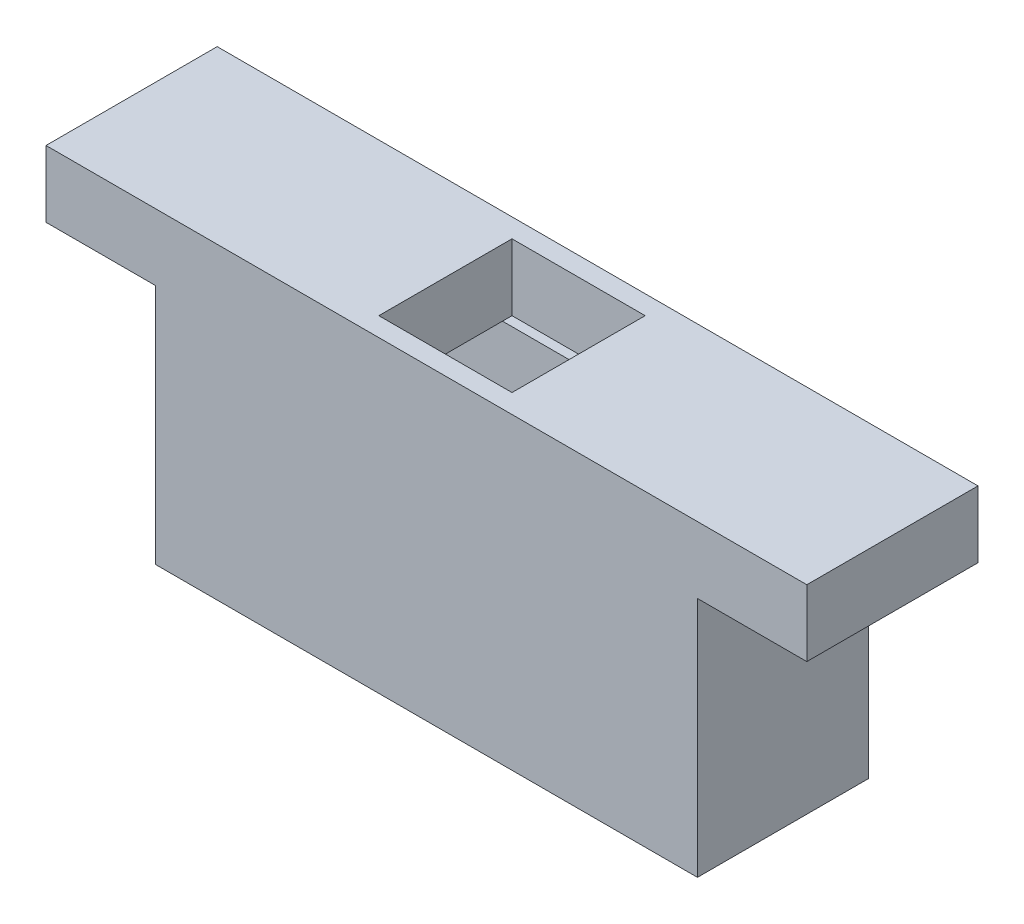
SolidWorks part; units mm, degrees
ref_plane "Front Plane" through (0, 0, 0) normal (0, 0, 1) x (1, 0, 0)
ref_plane "Top Plane" through (0, 0, 0) normal (0, 1, 0) x (1, 0, 0)
ref_plane "Right Plane" through (0, 0, 0) normal (1, 0, 0) x (0, 0, -1)
sketch "Sketch3" plane through (0, 0, 0) normal (0, 0, 1) x (1, 0, 0)
  line L0 (0, 0) -> (0, 25.4)
  line L1 (0, 25.4) -> (-11.5, 25.4)
  line L2 (-11.5, 25.4) -> (-11.5, 32.4)
  line L3 (-11.5, 32.4) -> (68.5, 32.4)
  line L4 (68.5, 32.4) -> (68.5, 25.4)
  line L5 (68.5, 25.4) -> (57, 25.4)
  line L6 (57, 25.4) -> (57, 0)
  line L7 (57, 0) -> (0, 0)
  dimension "D1" = 80
  dimension "D2" = 7
  dimension "D3" = 57
  dimension "D4" = 11.5
  dimension "D5" = 25.4
extrude "Boss-Extrude2" add sketch "Sketch3" along normal blind 18
sketch "Sketch4" plane through (0, 0, 0) normal (0, -1, 0) x (1, 0, 0)
  line L8 (0, 18) -> (57, 18) construction
  line L9 (2, 15) -> (55, 15)
  line L10 (2, 15) -> (2, 3)
  line L11 (2, 3) -> (55, 3)
  line L16 (55, 15) -> (55, 3)
  line L17 (0, 0) -> (57, 0) construction
  line L18 (0, 18) -> (0, 0) construction
  line L19 (57, 18) -> (57, 0) construction
  dimension "D1" = 3
  dimension "D2" = 3
  dimension "D3" = 2
  dimension "D4" = 2
extrude "Cut-Extrude2" cut sketch "Sketch4" against normal blind 25.4
sketch "Sketch5" plane through (0, 32.4, 0) normal (0, 1, 0) x (1, 0, 0)
  line L1 (21.5, -2) -> (35.5, -2)
  line L2 (21.5, -2) -> (21.5, -16)
  line L3 (21.5, -16) -> (35.5, -16)
  line L4 (35.5, -2) -> (35.5, -16)
  line L5 (68.5, 0) -> (-11.5, 0) construction
  line L7 (68.5, -18) -> (68.5, 0) construction
  dimension "D1" = 14
  dimension "D2" = 14
  dimension "D3" = 2
  dimension "D4" = 33
extrude "Cut-Extrude3" cut sketch "Sketch5" against normal blind 7
